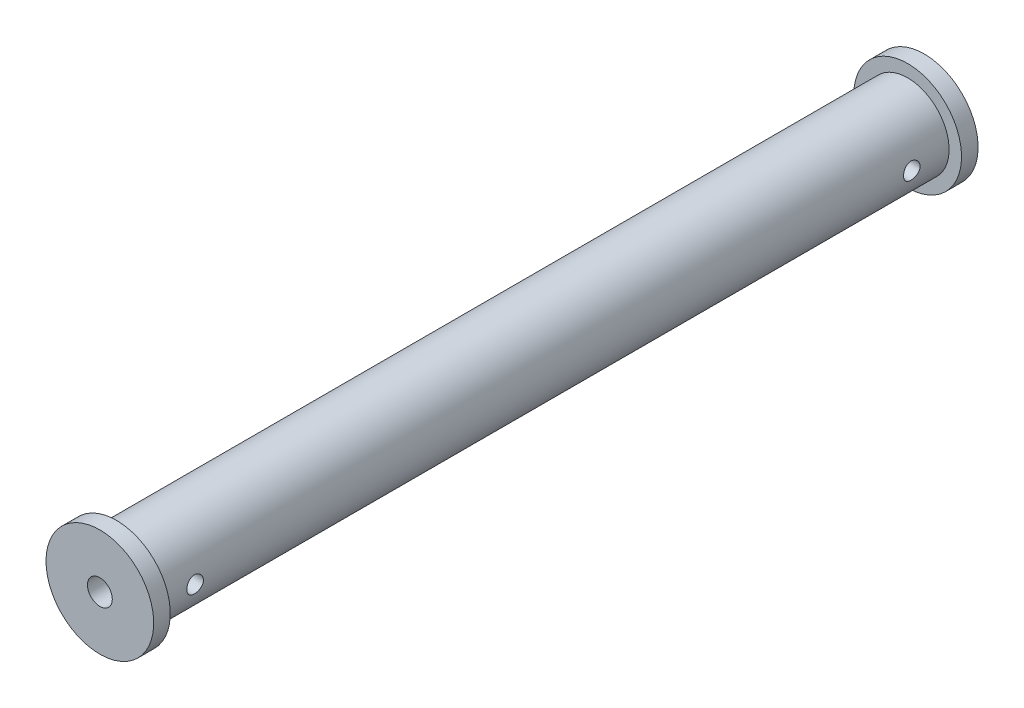
SolidWorks part; units mm, degrees
ref_plane "Front Plane" through (0, 0, 0) normal (0, 0, 1) x (1, 0, 0)
ref_plane "Top Plane" through (0, 0, 0) normal (0, 1, 0) x (1, 0, 0)
ref_plane "Right Plane" through (0, 0, 0) normal (1, 0, 0) x (0, 0, -1)
sketch "Sketch1" plane through (0, 0, 0) normal (0, 0, 1) x (1, 0, 0)
  circle A0 centre (0, 0) radius 10
  circle A1 centre (0, 0) radius 3
  dimension "D1" = 20
  dimension "D2" = 6
extrude "Boss-Extrude1" add sketch "Sketch1" along normal blind 199
sketch "Sketch2" plane through (0, 0, 0) normal (0, 0, -1) x (-1, 0, 0)
  circle A0 centre (0, 0) radius 13
  circle A1 centre (0, 0) radius 10 construction
  circle A2 centre (0, 0) radius 10
  dimension "D1" = 3
extrude "Boss-Extrude2" add sketch "Sketch2" against normal blind 4
ref_plane "Plane1" through (0, 0, 99.5) normal (0, 0, -1) x (-1, 0, 0)
mirror "Mirror1" about plane through (0, 0, 99.5) normal (0, 0, -1) of "Boss-Extrude2"
sketch "Sketch3" plane through (0, 0, 0) normal (0, 1, 0) x (1, 0, 0)
  line L0 (-10, -4) -> (-10, -195) construction
  line L1 (-10, -190) -> (-7, -190)
  line L2 (-10, -190) -> (-10, -182)
  line L3 (-10, -182) -> (-7, -182)
  line L4 (-7, -190) -> (-7, -182)
  line L5 (13, -195) -> (-13, -195) construction
  dimension "D1" = 8
  dimension "D2" = 3
  dimension "D3" = 5
extrude "Cut-Extrude1" cut sketch "Sketch3" against normal blind 25 and the other way blind 22
sketch "Sketch4" plane through (-7, 0, 0) normal (-1, 0, 0) x (0, 0, 1)
  line L0 (182, 0) -> (190, 0) construction
  line L3 (182, -7.1414) -> (182, 7.1414) construction
  line L4 (190, 7.1414) -> (190, -7.1414) construction
  circle A0 centre (186, 0) radius 1.5
  dimension "D1" = 3
hole_wizard "Ø4.0mm Clearance Dowel Hole1" positions "3DSketch1" profile "Sketch5" hole size "Ø4.0" standard "ISO" end condition through all
sketch3d "3DSketch1"
  point P0 (-7, 0, 186)
sketch "Sketch5" plane through (-7, 0, 186) normal (0, 1, 0) x (0, 0, 1)
  line L0 (0, 0) -> (0, 20)
  line L1 (0, 20) -> (2, 20)
  line L2 (2, 20) -> (2, 0)
  line L5 (2, 0) -> (0, 0)
  line L11 (0, -6.35) -> (0, 107.95) construction
  dimension "Thru Hole Dia." = 4
  dimension "Thru Hole Depth" = 20
mirror "Mirror2" about plane through (0, 0, 99.5) normal (0, 0, -1) of "Ø4.0mm Clearance Dowel Hole1", "Cut-Extrude1"
